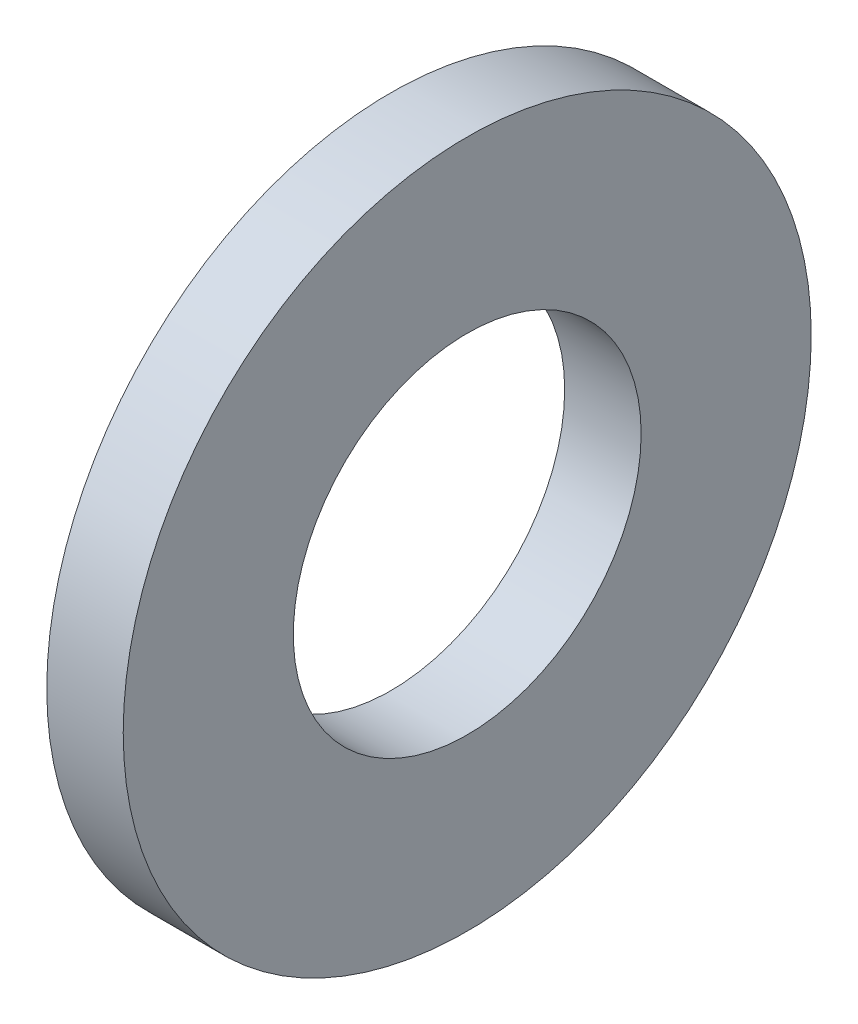
SolidWorks part; units mm, degrees
ref_plane "Plane1" through (0, 0, 0) normal (0, 0, 1) x (1, 0, 0)
ref_plane "Plane2" through (0, 0, 0) normal (0, 1, 0) x (1, 0, 0)
ref_plane "Plane3" through (0, 0, 0) normal (1, 0, 0) x (0, 0, -1)
sketch "Sketch1" plane through (0, 0, 0) normal (1, 0, 0) x (0, 0, -1)
  circle A0 centre (0, 0) radius 2.275
  circle A1 centre (0, 0) radius 4.5
  dimension "Insid_dia" = 4.55
  dimension "OutsideDia" = 9
extrude "Base-Extrude" add sketch "Sketch1" along normal blind 1
